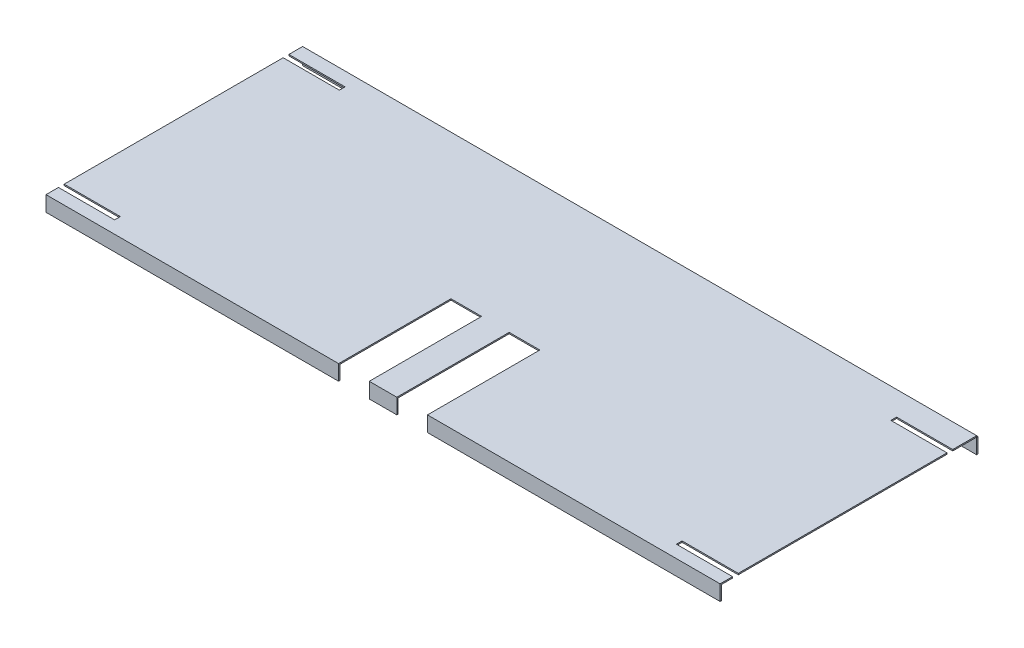
SolidWorks part; units mm, degrees
ref_plane "Front" through (0, 0, 0) normal (0, 0, 1) x (1, 0, 0)
ref_plane "Top" through (0, 0, 0) normal (0, 1, 0) x (1, 0, 0)
ref_plane "Right" through (0, 0, 0) normal (1, 0, 0) x (0, 0, -1)
sketch "Sketch1" plane through (0, 0, 0) normal (0, 1, 0) x (1, 0, 0)
  line L1 (0, 0) -> (838.2, 0)
  line L2 (0, 0) -> (0, -317.5)
  line L3 (0, -317.5) -> (838.2, -317.5)
  line L4 (838.2, 0) -> (838.2, -317.5)
  dimension "D1" = 838.2
  dimension "D2" = 317.5
extrude "Boss-Extrude1" add sketch "Sketch1" along normal blind 1.6002
sketch "Sketch3" plane through (0, 0, 317.5) normal (0, 0, 1) x (1, 0, 0)
  line L1 (0, 1.6002) -> (838.2, 1.6002)
  line L2 (0, 1.6002) -> (0, -17.4498)
  line L3 (0, -17.4498) -> (838.2, -17.4498)
  line L4 (838.2, 1.6002) -> (838.2, -17.4498)
  dimension "D1" = 19.05
extrude "Boss-Extrude2" add sketch "Sketch3" along normal blind 1.6002
sketch "Sketch2" plane through (0, 1.6002, 0) normal (0, 1, 0) x (1, 0, 0)
  line L1 (363.855, -179.4002) -> (363.855, -319.1002)
  line L2 (838.2, -319.1002) -> (0, -319.1002) construction
  line L3 (363.855, -319.1002) -> (401.955, -319.1002)
  line L4 (401.955, -319.1002) -> (401.955, -179.4002)
  line L5 (436.245, -179.4002) -> (436.245, -319.1002)
  line L6 (436.245, -319.1002) -> (474.345, -319.1002)
  line L7 (474.345, -319.1002) -> (474.345, -179.4002)
  line L8 (419.1, -319.1002) -> (419.1, -174.1645) construction
  line L9 (401.955, -249.2502) -> (419.1, -249.2502) construction
  line L11 (436.245, -249.2502) -> (419.1, -249.2502) construction
  line L17 (363.855, -179.4002) -> (401.955, -179.4002)
  line L21 (436.245, -179.4002) -> (474.345, -179.4002)
  dimension "D1" = 139.7
  dimension "D2" = 139.7
  dimension "D3" = 34.29
  dimension "D7" = 38.1
  dimension "D8" = 38.1
extrude "Cut-Extrude1" cut sketch "Sketch2" against normal up to next
sketch "Sketch4" plane through (0, 0, 0) normal (0, 0, -1) x (-1, 0, 0)
  line L1 (0, 0) -> (-838.2, 0)
  line L2 (0, 0) -> (0, -19.05)
  line L3 (0, -19.05) -> (-838.2, -19.05)
  line L4 (-838.2, 0) -> (-838.2, -19.05)
  dimension "D1" = 19.05
extrude "Boss-Extrude3" add sketch "Sketch4" along normal blind 1.6002
sketch "Sketch5" plane through (0, 1.6002, 0) normal (0, 1, 0) x (1, 0, 0)
  line L0 (0, 0) -> (0, -319.1002) construction
  line L1 (0, -17.0942) -> (69.85, -17.0942)
  line L2 (0, -17.0942) -> (0, -24.2062)
  line L3 (0, -24.2062) -> (69.85, -24.2062)
  line L4 (69.85, -17.0942) -> (69.85, -24.2062)
  line L5 (838.2, -319.1002) -> (838.2, 0) construction
  line L6 (0, -296.4942) -> (69.85, -296.4942)
  line L7 (0, -296.4942) -> (0, -303.6062)
  line L8 (0, -303.6062) -> (69.85, -303.6062)
  line L9 (69.85, -296.4942) -> (69.85, -303.6062)
  line L10 (838.2, -29.7942) -> (768.35, -29.7942)
  line L11 (838.2, -29.7942) -> (838.2, -36.9062)
  line L12 (838.2, -36.9062) -> (768.35, -36.9062)
  line L13 (768.35, -29.7942) -> (768.35, -36.9062)
  line L14 (363.855, -319.1002) -> (0, -319.1002) construction
  line L15 (838.2, -296.4942) -> (768.35, -296.4942)
  line L16 (838.2, -296.4942) -> (838.2, -303.6062)
  line L17 (838.2, -303.6062) -> (768.35, -303.6062)
  line L21 (768.35, -296.4942) -> (768.35, -303.6062)
  line L22 (838.2, -319.1002) -> (474.345, -319.1002) construction
  dimension "D5" = 15.494
  dimension "D6" = 272.288
  dimension "D9" = 69.85
  dimension "D1" = 7.112
  dimension "D2" = 7.112
  dimension "D3" = 7.112
  dimension "D4" = 7.112
  dimension "D7" = 69.85
  dimension "D8" = 69.85
  dimension "D10" = 69.85
  dimension "D11" = 15.494
  dimension "D12" = 259.588
extrude "Cut-Extrude2" cut sketch "Sketch5" against normal up to next (1.6002 mm away)
